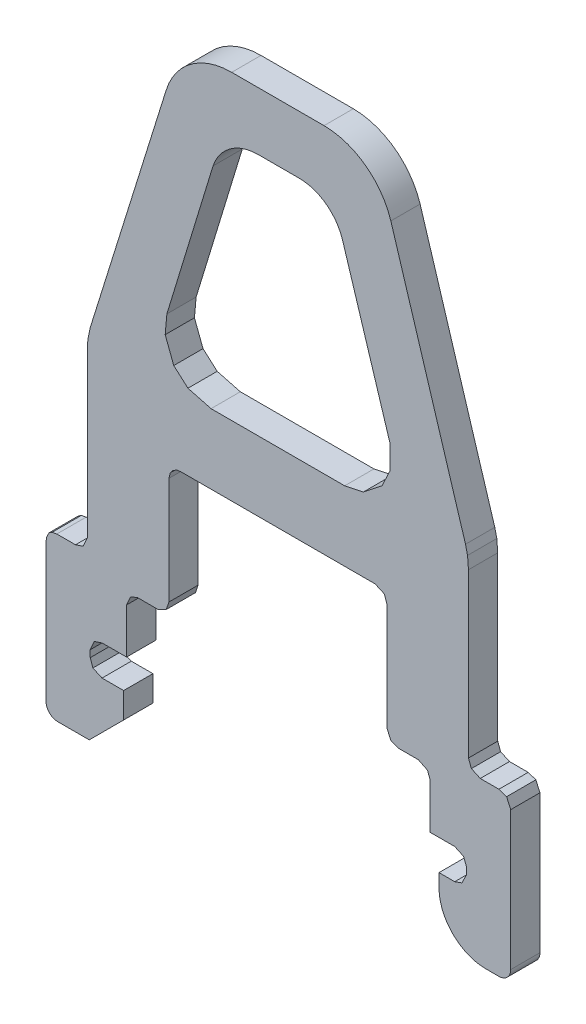
SolidWorks part; units mm, degrees
ref_plane "前视基准面" through (0, 0, 0) normal (0, 0, 1) x (1, 0, 0)
ref_plane "上视基准面" through (0, 0, 0) normal (0, 1, 0) x (1, 0, 0)
ref_plane "右视基准面" through (0, 0, 0) normal (1, 0, 0) x (0, 0, -1)
sketch "Model" plane through (0, 0, 0) normal (0, 0, 1) x (1, 0, 0)
  line L0 (490.799, 297.2696) -> (490.799, 293.801)
  line L2 (490.8836, 284.5373) -> (489.4877, 284.5373)
  line L153 (490.799, 293.801) -> (490.799, 292.0244)
  line L154 (490.2914, 291.5168) -> (489.4877, 291.5168)
  line L155 (489.0224, 291.0092) -> (489.0224, 285.0449)
  line L157 (490.8836, 284.5373) -> (492.3641, 286.0178)
  line L158 (492.3641, 286.0178) -> (492.3641, 287.1176)
  line L159 (492.3641, 287.1176) -> (491.4335, 287.1176)
  line L160 (490.9259, 287.6252) -> (490.9259, 287.9213)
  line L161 (491.4335, 288.4289) -> (492.491, 288.4289)
  line L162 (492.491, 288.4289) -> (492.491, 290.3747)
  line L163 (492.9563, 290.8823) -> (493.8446, 290.8823)
  line L164 (494.3099, 291.3899) -> (494.3099, 296.0006)
  line L165 (494.8175, 296.5082) -> (503.1929, 296.5082)
  line L166 (503.7005, 296.0006) -> (503.7005, 291.3899)
  line L167 (504.2081, 290.8823) -> (505.054, 290.8823)
  line L168 (505.5617, 290.3747) -> (505.5617, 288.4289)
  line L169 (505.5617, 288.4289) -> (506.6191, 288.4289)
  line L170 (507.1268, 287.9213) -> (507.1268, 287.6252)
  line L171 (506.6192, 287.1176) -> (505.9424, 287.1176)
  line L172 (505.9424, 287.1176) -> (505.9424, 286.5254)
  line L173 (507.9728, 284.5373) -> (508.5227, 284.5373)
  line L174 (509.0303, 285.0449) -> (509.0303, 291.0092)
  line L175 (508.5227, 291.5168) -> (507.719, 291.5168)
  line L176 (507.2114, 292.0244) -> (507.2114, 299.0462)
  line L177 (507.0845, 299.9345) -> (503.8697, 310.3826)
  line L178 (500.9933, 312.4976) -> (497.0171, 312.4976)
  line L179 (494.183, 310.3826) -> (490.9259, 299.9345)
  line L180 (490.799, 299.0462) -> (490.799, 297.2696)
  line L235 (499.0052, 310.0019) -> (499.8935, 310.0019)
  line L236 (501.797, 308.606) -> (503.8273, 302.0918)
  line L237 (501.8816, 299.5115) -> (499.0052, 299.5115)
  line L238 (499.0052, 299.5115) -> (496.1287, 299.5115)
  line L239 (494.2253, 302.0918) -> (496.2134, 308.606)
  line L240 (498.1592, 310.0019) -> (499.0052, 310.0019)
  line L479 (490.799, 292.0244) -> (490.6223, 291.6288)
  line L480 (490.6223, 291.6288) -> (490.2914, 291.5168)
  line L481 (489.4877, 291.5168) -> (489.2819, 291.477)
  line L482 (489.2819, 291.477) -> (489.1493, 291.3899)
  line L483 (489.1493, 291.3899) -> (489.047, 291.1767)
  line L484 (489.047, 291.1767) -> (489.0224, 291.0092)
  line L489 (491.4335, 287.1176) -> (491.0379, 287.2942)
  line L490 (491.0379, 287.2942) -> (490.9259, 287.6252)
  line L491 (490.9259, 287.9213) -> (491.1026, 288.3168)
  line L492 (491.1026, 288.3168) -> (491.4335, 288.4289)
  line L493 (492.491, 290.3747) -> (492.6603, 290.7565)
  line L494 (492.6603, 290.7565) -> (492.9563, 290.8823)
  line L495 (493.8446, 290.8823) -> (494.2015, 291.0589)
  line L496 (494.2015, 291.0589) -> (494.3099, 291.3899)
  line L497 (494.3099, 296.0006) -> (494.3746, 296.245)
  line L498 (494.3746, 296.245) -> (494.479, 296.3813)
  line L499 (494.479, 296.3813) -> (494.6536, 296.4836)
  line L500 (494.6536, 296.4836) -> (494.8175, 296.5082)
  line L501 (503.1929, 296.5082) -> (503.5885, 296.3315)
  line L502 (503.5885, 296.3315) -> (503.7005, 296.0006)
  line L503 (503.7005, 291.3899) -> (503.8772, 290.9943)
  line L504 (503.8772, 290.9943) -> (504.2081, 290.8823)
  line L505 (505.054, 290.8823) -> (505.4497, 290.6881)
  line L506 (505.4497, 290.6881) -> (505.5617, 290.3747)
  line L507 (506.6191, 288.4289) -> (507.001, 288.2522)
  line L508 (507.001, 288.2522) -> (507.1268, 287.9213)
  line L509 (507.1268, 287.6252) -> (506.9326, 287.2296)
  line L510 (506.9326, 287.2296) -> (506.6192, 287.1176)
  line L513 (509.0303, 291.0092) -> (508.8536, 291.4047)
  line L514 (508.8536, 291.4047) -> (508.5227, 291.5168)
  line L515 (507.719, 291.5168) -> (507.3372, 291.6934)
  line L516 (507.3372, 291.6934) -> (507.2114, 292.0244)
  line L517 (507.2114, 299.0462) -> (507.1716, 299.5611)
  line L518 (507.1716, 299.5611) -> (507.0845, 299.9345)
  line L519 (490.9259, 299.9345) -> (490.8236, 299.4508)
  line L520 (490.8236, 299.4508) -> (490.799, 299.0462)
  line L622 (503.8273, 302.0918) -> (503.8405, 301.0618)
  line L623 (503.8405, 301.0618) -> (503.4889, 300.3152)
  line L624 (503.4889, 300.3152) -> (502.6802, 299.6762)
  line L625 (502.6802, 299.6762) -> (501.8816, 299.5115)
  line L626 (496.1287, 299.5115) -> (495.1324, 299.7752)
  line L627 (495.1324, 299.7752) -> (494.5214, 300.3152)
  line L628 (494.5214, 300.3152) -> (494.153, 301.2825)
  line L629 (494.153, 301.2825) -> (494.2253, 302.0918)
  arc A0 (489.0224, 285.0449) -> (489.4877, 284.5373) centre (489.5319, 285.0449) ccw
  arc A1 (509.0303, 285.0449) -> (508.5227, 284.5373) centre (508.5227, 285.0449) cw
  arc A32 (505.9424, 286.5254) -> (507.9728, 284.5373) centre (507.9631, 286.5582) ccw
  arc A33 (503.8697, 310.3826) -> (500.9933, 312.4976) centre (500.9787, 309.4642) ccw
  arc A34 (497.0171, 312.4976) -> (494.183, 310.3826) centre (497.01, 309.5507) ccw
  arc A45 (501.797, 308.606) -> (499.8935, 310.0019) centre (499.9199, 308.0421) ccw
  arc A46 (498.1592, 310.0019) -> (496.2134, 308.606) centre (498.1562, 307.9519) ccw
extrude "凸台-拉伸1" add sketch "Model" along normal blind 1.26
